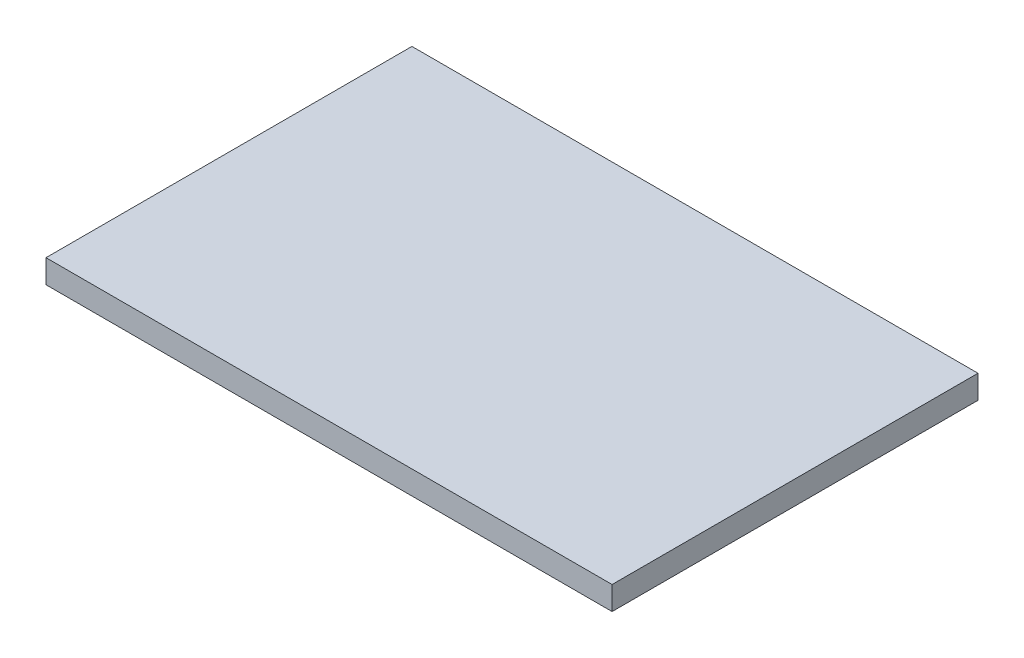
SolidWorks part; units mm, degrees
ref_plane "Front Plane" through (0, 0, 0) normal (0, 0, 1) x (1, 0, 0)
ref_plane "Top Plane" through (0, 0, 0) normal (0, 1, 0) x (1, 0, 0)
ref_plane "Right Plane" through (0, 0, 0) normal (1, 0, 0) x (0, 0, -1)
sketch "Sketch1" plane through (0, 0, 0) normal (0, 1, 0) x (1, 0, 0)
  line L1 (0, 0) -> (36.2, 0)
  line L2 (0, 0) -> (0, 23.4)
  line L3 (0, 23.4) -> (36.2, 23.4)
  line L4 (36.2, 0) -> (36.2, 23.4)
  dimension "D1" = 23.4
  dimension "D2" = 36.2
extrude "Boss-Extrude1" add sketch "Sketch1" along normal blind 1.5
